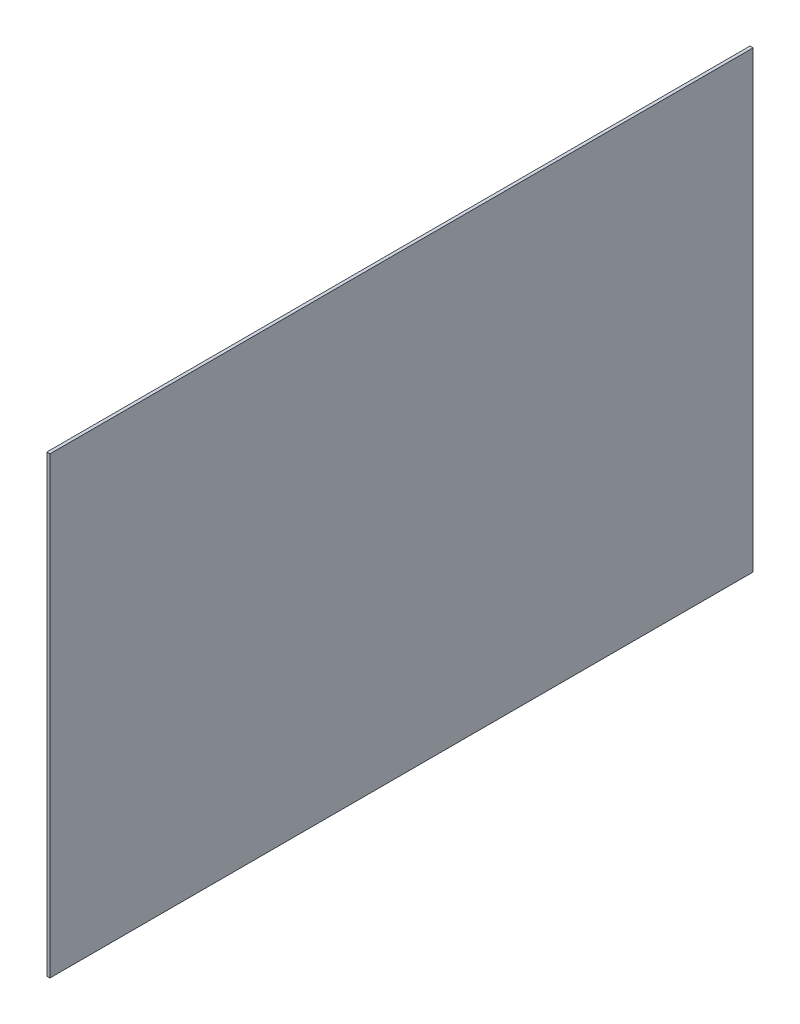
SolidWorks part; units mm, degrees
ref_plane "Front Plane" through (0, 0, 0) normal (0, 0, 1) x (1, 0, 0)
ref_plane "Top Plane" through (0, 0, 0) normal (0, 1, 0) x (1, 0, 0)
ref_plane "Right Plane" through (0, 0, 0) normal (1, 0, 0) x (0, 0, -1)
sketch "Sketch1" plane through (0, 0, 0) normal (1, 0, 0) x (0, 0, -1)
  line L1 (-109.3524, 387.5957) -> (790.6476, 387.5957)
  line L2 (-109.3524, 387.5957) -> (-109.3524, -193.4043)
  line L3 (-109.3524, -193.4043) -> (790.6476, -193.4043)
  line L4 (790.6476, 387.5957) -> (790.6476, -193.4043)
extrude "Boss-Extrude1" add sketch "Sketch1" along normal blind 4
